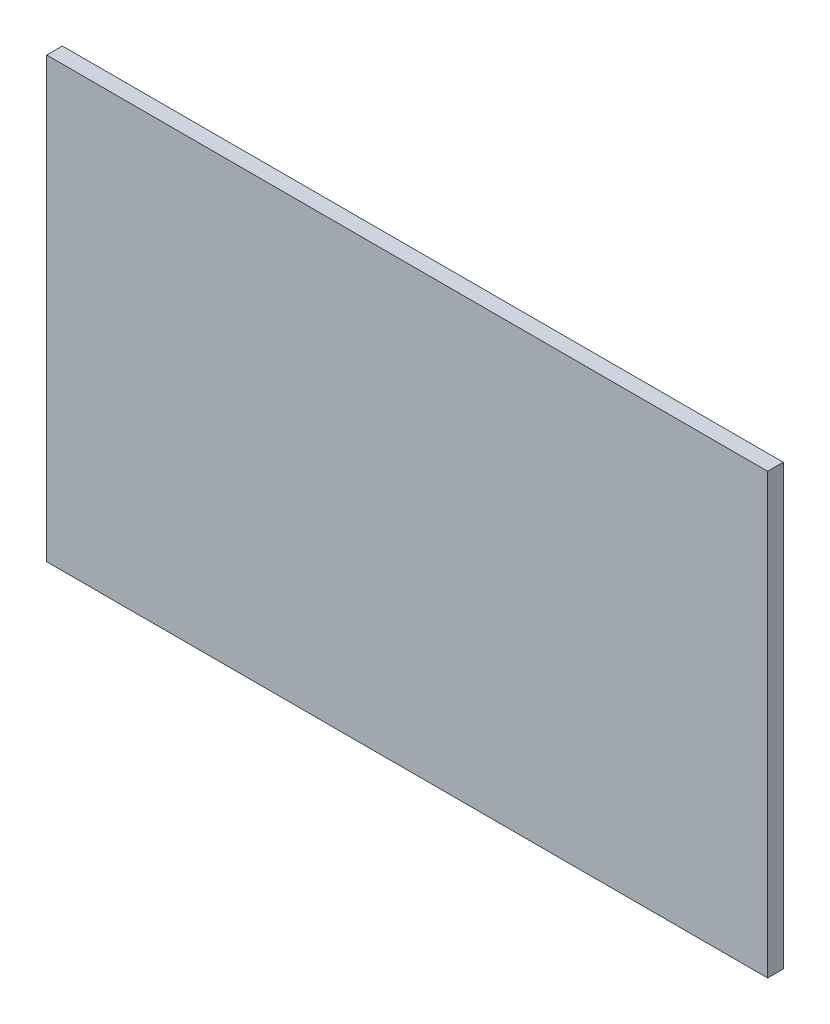
SolidWorks part; units mm, degrees
ref_plane "Plan de face" through (0, 0, 0) normal (0, 0, 1) x (1, 0, 0)
ref_plane "Plan de dessus" through (0, 0, 0) normal (0, 1, 0) x (1, 0, 0)
ref_plane "Plan de droite" through (0, 0, 0) normal (1, 0, 0) x (0, 0, -1)
sketch "Sketch1" plane through (0, 0, 0) normal (0, 0, 1) x (1, 0, 0)
  line L0 (0, 70) -> (0, -70) construction
  line L1 (-115, 70) -> (115, 70)
  line L2 (-115, 70) -> (-115, -70)
  line L3 (-115, -70) -> (115, -70)
  line L4 (115, 70) -> (115, -70)
  point P7 (0, 0)
  dimension "D1" = 230
  dimension "D2" = 140
extrude "Boss-Extrude1" add sketch "Sketch1" along normal blind 5
sketch "Sketch3" plane through (0, 0, 5) normal (0, 0, 1) x (1, 0, 0)
  line L0 (0, 70) -> (0, -70) construction
  line L1 (115, 70) -> (-115, 70) construction
  line L2 (-115, -70) -> (115, -70) construction
  line L3 (-115, 70) -> (-115, -70) construction
  line L4 (-110, 47) -> (-95, 47)
  line L5 (-110, 47) -> (-110, -47)
  line L6 (-110, -47) -> (-95, -47)
  line L7 (-95, 47) -> (-95, -47)
  line L8 (-115, 0) -> (115, 0) construction
  line L9 (115, -70) -> (115, 70) construction
  line L10 (95, 47) -> (95, -47)
  line L11 (110, -47) -> (95, -47)
  line L12 (110, 47) -> (110, -47)
  line L13 (110, 47) -> (95, 47)
  line L14 (22, 58) -> (22, 70)
  line L15 (-22, -58) -> (22, -58)
  line L16 (-22, -58) -> (-22, -70)
  line L17 (-22, -70) -> (22, -70)
  line L18 (22, -58) -> (22, -70)
  line L19 (-22, 70) -> (22, 70)
  line L20 (-22, 58) -> (-22, 70)
  line L21 (-22, 58) -> (22, 58)
  dimension "D1" = 15
  dimension "D2" = 5
  dimension "D3" = 94
  dimension "D4" = 44
  dimension "D5" = 12
sketch "Sketch4" plane through (0, 0, 0) normal (0, 0, 1) x (1, 0, 0)
  line L0 (0, 70) -> (0, -70) construction
  line L4 (-110, 47) -> (-95, 47)
  line L5 (-110, 47) -> (-110, -47)
  line L6 (-110, -47) -> (-95, -47)
  line L7 (-95, 47) -> (-95, -47)
  line L8 (-115, 0) -> (115, 0) construction
  dimension "D1" = 15
  dimension "D3" = 94
sketch "Sketch5" plane through (0, 0, 0) normal (0, 1, 0) x (1, 0, 0)
  line L0 (-100, 0) -> (-100, 30)
  line L1 (-115, 0) -> (115, 0) construction
  line L2 (-100, 30) -> (-60, 70)
  line L3 (-60, 70) -> (60, 70)
  line L4 (60, 70) -> (100, 30)
  line L5 (100, 30) -> (100, 0)
  line L6 (0, 70) -> (0, 0) construction
  dimension "D1" = 70
  dimension "D2" = 30
  dimension "D3" = 15
  dimension "D4" = 40
